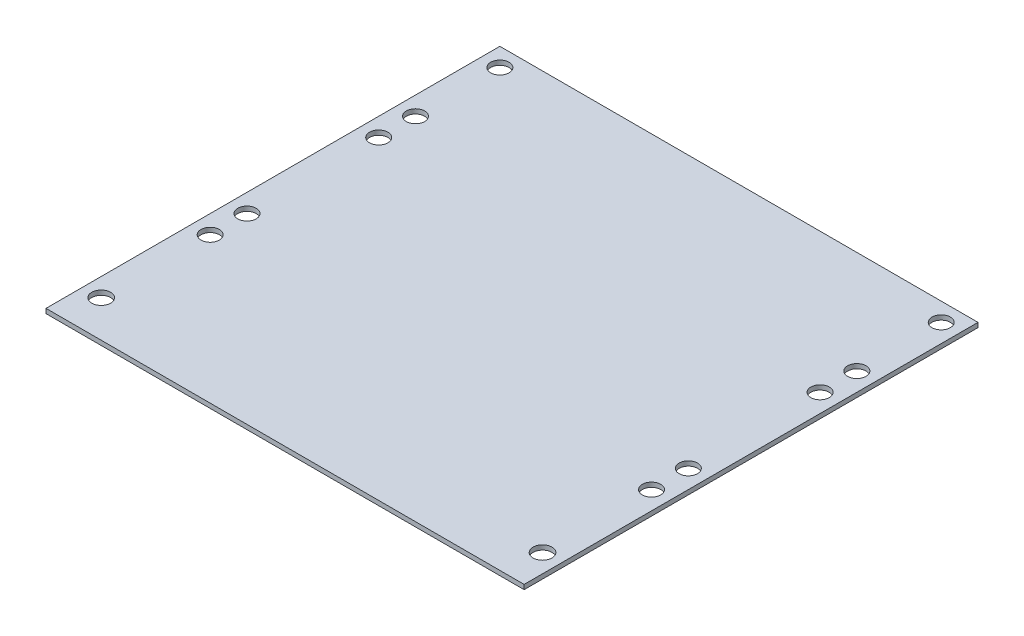
SolidWorks part; units mm, degrees
material "PE High Density"
ref_plane "Front Plane" through (0, 0, 0) normal (0, 0, 1) x (1, 0, 0)
ref_plane "Top Plane" through (0, 0, 0) normal (0, 1, 0) x (1, 0, 0)
ref_plane "Right Plane" through (0, 0, 0) normal (1, 0, 0) x (0, 0, -1)
sketch "Sketch1" plane through (0, 0, 0) normal (0, 1, 0) x (1, 0, 0)
  line L0 (6.35, 12.7) -> (6.35, 56.697) construction
  line L1 (0, 0) -> (165.1, 0)
  line L2 (0, 0) -> (0, 156.718)
  line L3 (0, 156.718) -> (165.1, 156.718)
  line L4 (165.1, 0) -> (165.1, 156.718)
  line L5 (6.35, 12.7) -> (6.35, 61.3276) construction
  line L6 (6.35, 56.697) -> (6.35, 124.968) construction
  line L7 (6.35, 124.968) -> (6.35, 114.8866) construction
  line L8 (6.35, 124.968) -> (6.35, 156.718) construction
  line L9 (82.55, 156.718) -> (82.55, 100.5876) construction
  line L10 (158.75, 124.968) -> (158.75, 114.8866) construction
  line L11 (158.75, 56.697) -> (158.75, 124.968) construction
  circle A0 centre (6.35, 12.7) radius 3.2639
  circle A6 centre (6.35, 150.368) radius 3.175
  circle A7 centre (158.75, 12.7) radius 3.2639
  circle A12 centre (158.75, 150.368) radius 3.175
  circle A13 centre (6.35, 121.2366) radius 3.175
  circle A14 centre (6.35, 108.5366) radius 3.175
  circle A15 centre (6.35, 63.047) radius 3.175
  circle A16 centre (6.35, 50.347) radius 3.175
  circle A17 centre (158.75, 50.347) radius 3.175
  circle A18 centre (158.75, 63.047) radius 3.175
  circle A19 centre (158.75, 108.5366) radius 3.175
  circle A20 centre (158.75, 121.2366) radius 3.175
  dimension "D2" = 6.35
  dimension "D3" = 6.35
  dimension "D4" = 6.5278
  dimension "D6" = 12.7
  dimension "D5" = 35.4814
  dimension "D7" = 58.1896
  dimension "D8" = 6.35
  dimension "D9" = 6.35
  dimension "D11" = 6.35
  dimension "D12" = 6.35
  dimension "D14" = 6.35
  dimension "D16" = 6.35
  dimension "D17" = 6.35
  dimension "D10" = 6.35
  dimension "D13" = 6.35
  dimension "D1" = 165.1
  dimension "D15" = 156.718
extrude "Boss-Extrude1" add sketch "Sketch1" along normal blind 1.5875
